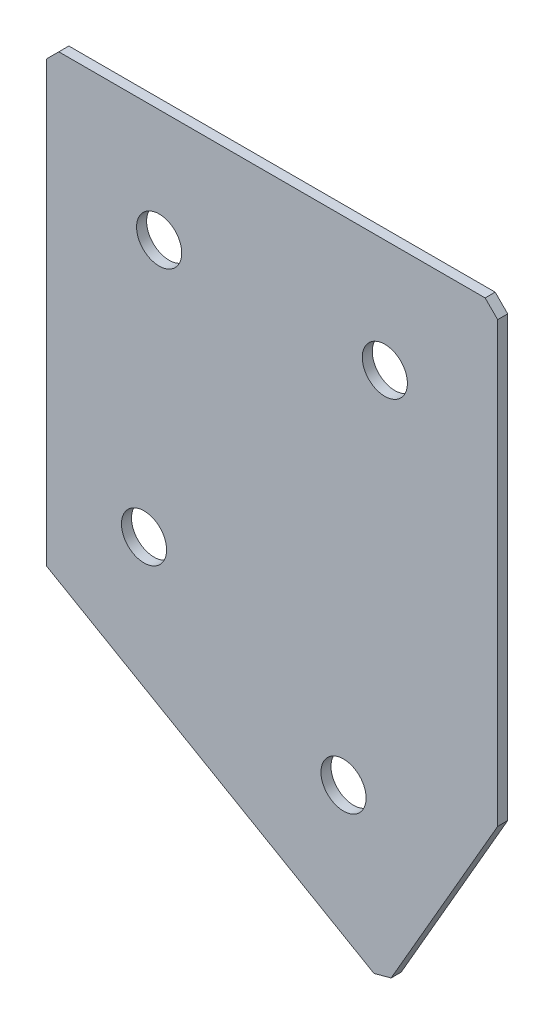
SolidWorks part; units mm, degrees
material "Простая углеродистая сталь"
ref_plane "Спереди" through (0, 0, 0) normal (0, 0, 1) x (1, 0, 0)
ref_plane "Сверху" through (0, 0, 0) normal (0, 1, 0) x (1, 0, 0)
ref_plane "Справа" through (0, 0, 0) normal (1, 0, 0) x (0, 0, -1)
sketch "Эскиз3" plane through (0, 0, 0) normal (0, 0, -1) x (1, 0, 0)
  line L0 (0, 0) -> (90, 0)
  line L1 (90, 0) -> (90, 90)
  line L2 (0, 0) -> (0, 90)
  line L3 (0, 90) -> (67.5, 128.9711)
  line L4 (67.5, 128.9711) -> (90, 90)
  dimension "D1" = 90
  dimension "D2" = 90
  dimension "D3" = 45
  dimension "D4" = 30
  dimension "D5" = 90
extrude "Бобышка-Вытянуть1" add sketch "Эскиз3" along normal blind 2
hole_wizard "Отверстие с зазором M81" positions "Эскиз4" profile "Эскиз5" hole size "M8" standard "DIN" end condition through all
sketch "Эскиз4" plane through (0, 0, -2) normal (0, 0, -1) x (1, 0, 0)
  line L0 (19.4856, 75.2692) -> (59.2644, 98.2356) construction
  line L2 (67.5, 128.9711) -> (0, 90) construction
  line L3 (22.5, 22.5) -> (67.5, 22.5) construction
  line L5 (0, 0) -> (90, 0) construction
  line L6 (0, 90) -> (0, 0) construction
  line L7 (90, 0) -> (90, 90) construction
  line L8 (90, 90) -> (67.5, 128.9711) construction
  line L9 (19.4856, 75.2692) -> (0, 64.0192) construction
  point P0 (22.5, 22.5)
  point P2 (67.5, 22.5)
  point P4 (19.4856, 75.2692)
  point P6 (59.2644, 98.2356)
  dimension "D1" = 22.5
  dimension "D2" = 22.5
  dimension "D3" = 22.5
  dimension "D4" = 22.5
  dimension "D5" = 22.5
  dimension "D6" = 22.5
  dimension "D7" = 45.9327
  dimension "D8" = 45
sketch "Эскиз5" plane through (22.5, -22.5, -2) normal (1, 0, 0) x (0, 1, 0)
  line L0 (0, 0) -> (0, 2)
  line L1 (0, 2) -> (4.5, 2)
  line L2 (4.5, 2) -> (4.5, 0)
  line L5 (4.5, 0) -> (0, 0)
  line L11 (0, -6.35) -> (0, 107.95) construction
  dimension "Диаметр сквозного отверстия" = 9
  dimension "Глубина сквозного отверстия" = 2
chamfer "Фаска1" distance 2.5 distance2 2.5 3 edges at (67.5, -128.9711, -1) (90, 0, -1) (0, 0, -1)
